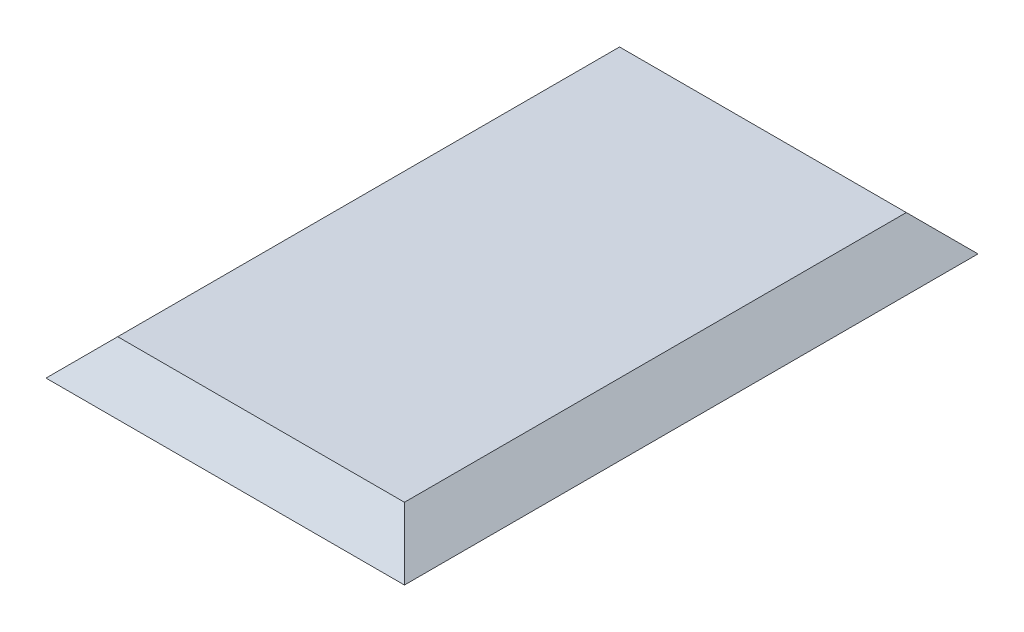
SolidWorks part; units mm, degrees
ref_plane "Front Plane" through (0, 0, 0) normal (0, 0, 1) x (1, 0, 0)
ref_plane "Top Plane" through (0, 0, 0) normal (0, 1, 0) x (1, 0, 0)
ref_plane "Right Plane" through (0, 0, 0) normal (1, 0, 0) x (0, 0, -1)
sketch "Sketch1" plane through (0, 0, 0) normal (0, 1, 0) x (1, 0, 0)
  line L1 (-25, 40) -> (25, 40)
  line L2 (-25, 40) -> (-25, -40)
  line L3 (-25, -40) -> (25, -40)
  line L4 (25, 40) -> (25, -40)
  line L5 (-25, 40) -> (25, -40) construction
  line L6 (-25, -40) -> (25, 40) construction
  point P0 (0, 0)
  dimension "D1" = 50
  dimension "D2" = 80
extrude "Boss-Extrude1" add sketch "Sketch1" along normal blind 5
sketch "Sketch2" plane through (0, 0, 0) normal (0, 0, 1) x (1, 0, 0)
  line L0 (-25, 0) -> (-20, 5)
  line L1 (25, 0) -> (20, 5)
  line L2 (-25, 0) -> (25, 0) construction
  line L3 (-25, 5) -> (25, 5) construction
  line L4 (-25, 5) -> (-20, 5)
  line L5 (-25, 5) -> (-25, 0) construction
  line L6 (-25, 5) -> (-25, 0)
  line L7 (25, 5) -> (25, 0) construction
  line L8 (25, 5) -> (25, 0)
  line L9 (20, 5) -> (25, 5)
  dimension "D1" = 45
  dimension "D2" = 45
extrude "Cut-Extrude1" cut sketch "Sketch2" against normal through all both and the other way through all
sketch "Sketch3" plane through (0, 0, 0) normal (1, 0, 0) x (0, 0, -1)
  line L0 (-40, 0) -> (-35, 5)
  line L1 (40, 0) -> (35, 5)
  line L2 (-40, 0) -> (40, 0) construction
  line L3 (40, 5) -> (40, 0) construction
  line L4 (-40, 5) -> (-40, 0) construction
  line L5 (40, 5) -> (-40, 5) construction
  line L6 (40, 5) -> (40, 0)
  line L7 (-40, 5) -> (-40, 0)
  line L8 (40, 5) -> (35, 5)
  line L9 (-35, 5) -> (-40, 5)
  dimension "D1" = 45
  dimension "D2" = 45
extrude "Cut-Extrude2" cut sketch "Sketch3" against normal through all both and the other way through all
